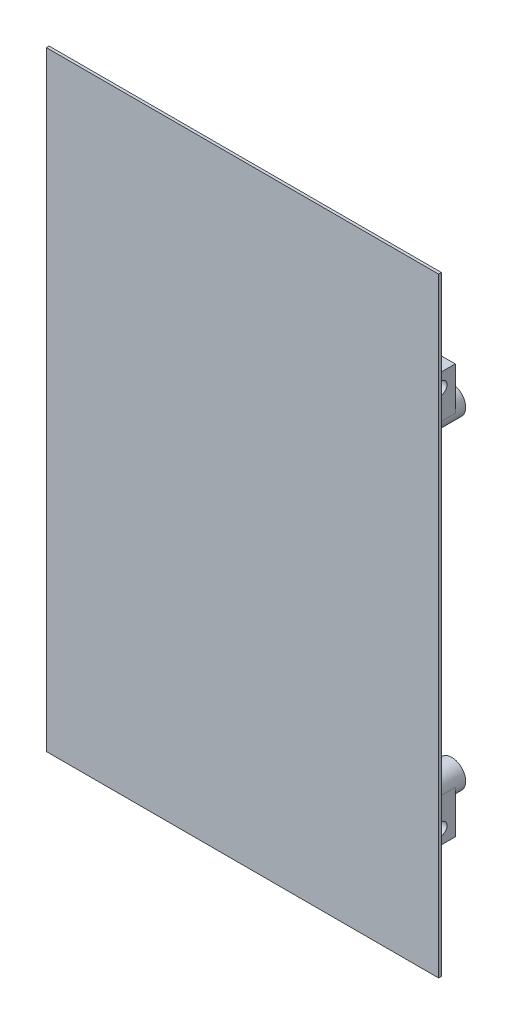
SolidWorks part; units mm, degrees
ref_plane "Front Plane" through (0, 0, 0) normal (0, 0, 1) x (1, 0, 0)
ref_plane "Top Plane" through (0, 0, 0) normal (0, 1, 0) x (1, 0, 0)
ref_plane "Right Plane" through (0, 0, 0) normal (1, 0, 0) x (0, 0, -1)
sketch "Sketch1" plane through (0, 0, 0) normal (0, 0, 1) x (1, 0, 0)
  line L1 (109, 161.3091) -> (-4, 161.3091)
  line L2 (109, 161.3091) -> (109, -14.3091)
  line L3 (109, -14.3091) -> (-4, -14.3091)
  line L4 (-4, 161.3091) -> (-4, -14.3091)
extrude "Boss-Extrude1" add sketch "Sketch1" along normal blind 0.8
sketch "Sketch2" plane through (0, 0, 0) normal (0, 0, -1) x (-1, 0, 0)
  circle A0 centre (-7.2, 26.85) radius 2 construction
  circle A1 centre (-101, 26.85) radius 2 construction
  circle A2 centre (-101, 120.15) radius 2 construction
  circle A3 centre (-7.2, 120.15) radius 2 construction
  circle A4 centre (-7.2, 26.85) radius 2
  circle A5 centre (-101, 26.85) radius 2
  circle A6 centre (-101, 120.15) radius 2
  circle A7 centre (-7.2, 120.15) radius 2
  circle A8 centre (-7.2, 120.15) radius 4
  circle A9 centre (-7.2, 26.85) radius 4
  circle A10 centre (-101, 26.85) radius 4
  circle A11 centre (-101, 120.15) radius 4
  dimension "D1" = 8
extrude "Boss-Extrude2" add sketch "Sketch2" along normal up to surface (11 mm away)
sketch "Sketch3" plane through (0, 0, 0) normal (0, 0, -1) x (-1, 0, 0)
  line L0 (-101, 120.15) -> (-7.2, 120.15) construction
  line L1 (-8.9321, 123.15) -> (-9.8458, 123.15)
  line L2 (-10.6641, 120.15) -> (-8.9321, 117.15)
  line L3 (-8.9321, 117.15) -> (-5.4679, 117.15)
  line L4 (-5.4679, 117.15) -> (-3.7359, 120.15)
  line L5 (-3.7359, 120.15) -> (-5.4679, 123.15)
  line L6 (-5.4679, 123.15) -> (-8.9321, 123.15)
  line L7 (-8.9321, 123.15) -> (-10.6641, 120.15)
  line L8 (-8.9321, 117.15) -> (-9.8458, 117.15)
  line L9 (-52.5, 161.3091) -> (-52.5, -14.3091) construction
  line L10 (-109, 161.3091) -> (4, 161.3091) construction
  line L11 (4, -14.3091) -> (-109, -14.3091) construction
  line L12 (-99.2679, 123.15) -> (-98.3542, 123.15)
  line L13 (-97.5359, 120.15) -> (-99.2679, 123.15)
  line L14 (-99.2679, 123.15) -> (-102.7321, 123.15)
  line L15 (-102.7321, 123.15) -> (-104.4641, 120.15)
  line L16 (-104.4641, 120.15) -> (-102.7321, 117.15)
  line L17 (-102.7321, 117.15) -> (-99.2679, 117.15)
  line L18 (-99.2679, 117.15) -> (-97.5359, 120.15)
  line L19 (-97.5359, 26.85) -> (-99.2679, 29.85)
  line L20 (-109, 73.5) -> (4, 73.5) construction
  line L21 (-109, -14.3091) -> (-109, 161.3091) construction
  line L22 (4, 161.3091) -> (4, -14.3091) construction
  line L23 (-8.9321, 29.85) -> (-9.8458, 29.85)
  line L24 (-8.9321, 29.85) -> (-5.4679, 29.85)
  line L25 (-10.6641, 26.85) -> (-8.9321, 29.85)
  line L26 (-3.7359, 26.85) -> (-5.4679, 23.85)
  line L27 (-5.4679, 29.85) -> (-3.7359, 26.85)
  line L28 (-8.9321, 23.85) -> (-10.6641, 26.85)
  line L29 (-5.4679, 23.85) -> (-8.9321, 23.85)
  line L30 (-8.9321, 23.85) -> (-9.8458, 23.85)
  line L31 (-99.2679, 29.85) -> (-102.7321, 29.85)
  line L32 (-102.7321, 29.85) -> (-104.4641, 26.85)
  line L33 (-104.4641, 26.85) -> (-102.7321, 23.85)
  line L34 (-102.7321, 23.85) -> (-99.2679, 23.85)
  line L35 (-99.2679, 23.85) -> (-97.5359, 26.85)
  line L36 (-99.2679, 117.15) -> (-98.3542, 117.15)
  line L37 (-99.2679, 29.85) -> (-98.3542, 29.85)
  line L38 (-99.2679, 23.85) -> (-98.3542, 23.85)
  circle A0 centre (-7.2, 120.15) radius 3 construction
  circle A1 centre (-7.2, 120.15) radius 4 construction
  circle A2 centre (-7.2, 120.15) radius 4 construction
  circle A3 centre (-101, 120.15) radius 3 construction
  circle A4 centre (-101, 26.85) radius 3 construction
  circle A5 centre (-101, 26.85) radius 4 construction
  circle A6 centre (-101, 120.15) radius 4 construction
  circle A7 centre (-101, 26.85) radius 4
  circle A8 centre (-101, 120.15) radius 4
  circle M15 centre (-101, 120.15) radius 4
  circle M16 centre (-101, 26.85) radius 4
  circle M17 centre (-7.2, 26.85) radius 4
  circle M18 centre (-7.2, 120.15) radius 4
  dimension "D1" = 6
extrude "Cut-Extrude1" cut sketch "Sketch3" along normal blind 3.5 contours L6 L7 L2 L3 L4 L5 | L8 L2 L7 L1 M18 | L17 L18 L13 L14 L15 L16 | L18 L36 L12 L13 M15 | L35 L38 L37 L19 M16 | L34 L35 L19 L31 L32 L33 | L29 L26 L27 L24 L25 L28 | L30 L28 L25 L23 M17
sketch "Sketch4" plane through (0, 0, 0) normal (0, 0, -1) x (-1, 0, 0)
  line L0 (-105, -14.3091) -> (-105, 161.3091) construction
  line L1 (-105, 14.5) -> (-100, 14.5)
  line L2 (-105, 14.5) -> (-105, 22.5)
  line L3 (-105, 22.5) -> (-100, 22.5)
  line L4 (-100, 14.5) -> (-100, 22.5)
  line L5 (-100, 18.5) -> (-105, 18.5) construction
  line L6 (-105, 26.85) -> (-105, 22.5)
  line L7 (-101, 120.15) -> (-101, 26.85) construction
  line L8 (-100, 22.5) -> (-100, 22.977)
  line L9 (-109, 73.5) -> (4, 73.5) construction
  line L10 (-109, -14.3091) -> (-109, 161.3091) construction
  line L11 (4, 161.3091) -> (4, -14.3091) construction
  line L12 (-105, 120.15) -> (-105, 124.5)
  line L13 (-105, 132.5) -> (-105, 124.5)
  line L14 (-105, 132.5) -> (-100, 132.5)
  line L15 (-109, 18.5) -> (-105, 18.5) construction
  line L16 (-105, 124.5) -> (-100, 124.5)
  line L17 (-100, 132.5) -> (-100, 124.5)
  line L18 (-100, 124.5) -> (-100, 124.023)
  line L19 (-52.5, 161.3091) -> (-52.5, -14.3091) construction
  line L20 (-109, 161.3091) -> (4, 161.3091) construction
  line L21 (4, -14.3091) -> (-109, -14.3091) construction
  line L22 (-105, 161.3091) -> (-105, -14.3091) construction
  line L23 (0, 161.3091) -> (0, -14.3091) construction
  line L24 (0, 14.5) -> (-5, 14.5)
  line L25 (0, 22.5) -> (-5, 22.5)
  line L26 (0, 14.5) -> (0, 22.5)
  line L27 (0, 132.5) -> (0, 124.5)
  line L28 (0, 124.5) -> (-5, 124.5)
  line L29 (0, 132.5) -> (-5, 132.5)
  line L30 (-5, 132.5) -> (-5, 124.5)
  line L31 (-3.2, 120.15) -> (-3.2, 124.5)
  line L32 (-5, 124.5) -> (-5, 123.4907)
  line L33 (-5, 14.5) -> (-5, 23.5093)
  line L34 (-3.2, 26.85) -> (-3.2, 22.5)
  arc A0 (-98.3542, 29.85) -> (-98.3542, 23.85) centre (-101, 26.85) ccw construction
  arc A1 (-9.8458, 117.15) -> (-9.8458, 123.15) centre (-7.2, 120.15) ccw construction
  arc A2 (-98.3542, 29.85) -> (-98.3542, 23.85) centre (-101, 26.85) ccw construction
  circle A3 centre (-7.2, 120.15) radius 4 construction
  arc A4 (-9.8458, 23.85) -> (-9.8458, 29.85) centre (-7.2, 26.85) ccw construction
  point P26 (-101, 73.5)
  dimension "D1" = 8
  dimension "D2" = 5
extrude "Boss-Extrude3" add sketch "Sketch4" along normal blind 8
sketch "Sketch5" plane through (105, 0, 0) normal (-1, 0, 0) x (0, 0, 1)
  line L0 (-4, 120.15) -> (-4, 26.85) construction
  line L1 (-8, 120.15) -> (0, 120.15) construction
  line L2 (-8, 26.85) -> (0, 26.85) construction
  line L3 (-4, 73.5) -> (0, 73.5) construction
  line L4 (0, -14.3091) -> (0, 161.3091) construction
  circle A0 centre (-3.8964, 128.5) radius 1.75
  circle A1 centre (-3.8964, 18.5) radius 1.75
  circle A2 centre (-3.8964, 18.5) radius 2.9 construction
  dimension "D1" = 3.5
extrude "Cut-Extrude2" cut sketch "Sketch5" along normal up to surface (105 mm away) up to face at (0, 18.5, -4)
sketch "Sketch6" plane through (100, 0, 0) normal (-1, 0, 0) x (0, 0, 1)
  line L0 (-4, 120.15) -> (-4, 26.85) construction
  line L1 (-3.8964, 21.9641) -> (-6.8964, 20.2321)
  line L2 (-6.8964, 20.2321) -> (-6.8964, 16.7679)
  line L3 (-6.8964, 16.7679) -> (-3.8964, 15.0359)
  line L4 (-3.8964, 15.0359) -> (-0.8964, 16.7679)
  line L5 (-0.8964, 16.7679) -> (-0.8964, 20.2321)
  line L6 (-0.8964, 20.2321) -> (-3.8964, 21.9641)
  line L7 (-8, 120.15) -> (0, 120.15) construction
  line L8 (-8, 26.85) -> (0, 26.85) construction
  line L9 (-4, 73.5) -> (0, 73.5) construction
  line L10 (0, -14.3091) -> (0, 161.3091) construction
  line L11 (-0.8964, 130.2321) -> (-0.8964, 126.7679)
  line L12 (-0.8964, 126.7679) -> (-3.8964, 125.0359)
  line L13 (-3.8964, 125.0359) -> (-6.8964, 126.7679)
  line L14 (-6.8964, 126.7679) -> (-6.8964, 130.2321)
  line L15 (-6.8964, 130.2321) -> (-3.8964, 131.9641)
  line L16 (-3.8964, 131.9641) -> (-0.8964, 130.2321)
  circle A0 centre (-3.8964, 18.5) radius 3 construction
  dimension "D1" = 6
extrude "Cut-Extrude3" cut sketch "Sketch6" against normal blind 2.5
ref_plane "Plane7" through (52.5, 0, 0) normal (-1, 0, 0) x (0, 0, 1)
mirror "Mirror1" about plane through (52.5, 0, 0) normal (-1, 0, 0) of "Cut-Extrude3"
